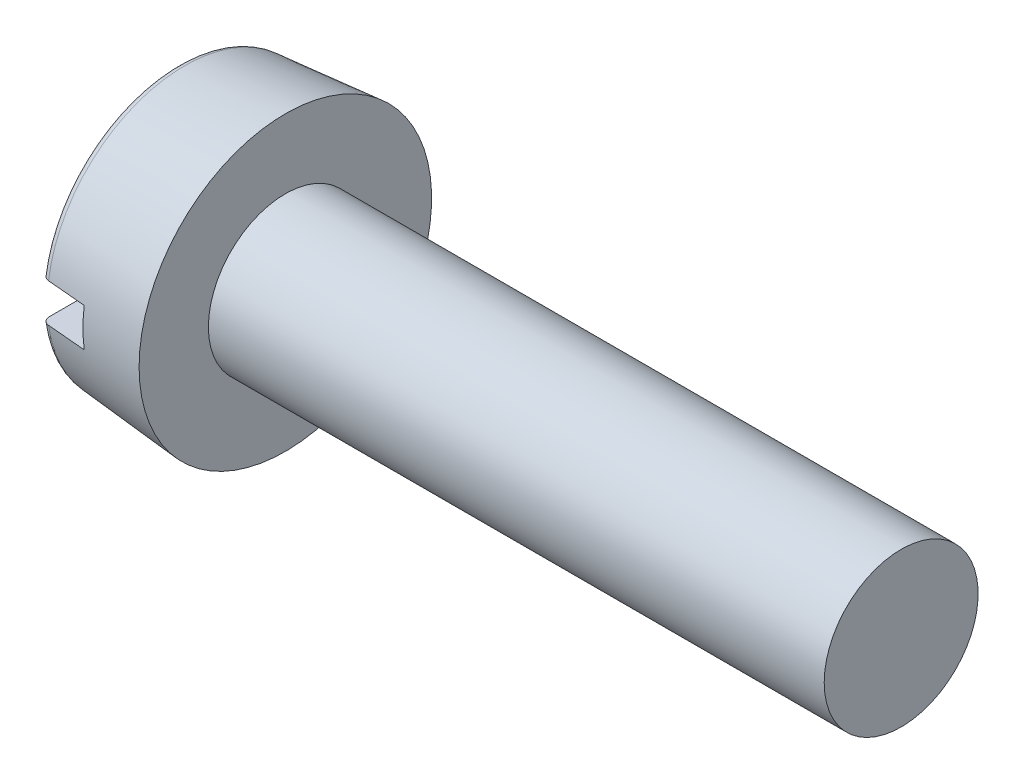
SolidWorks part; units mm, degrees
ref_plane "Plane1" through (0, 0, 0) normal (0, 0, 1) x (1, 0, 0)
ref_plane "Plane2" through (0, 0, 0) normal (0, 1, 0) x (1, 0, 0)
ref_plane "Plane3" through (0, 0, 0) normal (1, 0, 0) x (0, 0, -1)
sketch "BodySke" plane through (0, 0, 0) normal (0, 0, 1) x (1, 0, 0)
  line L0 (1.4, 1) -> (1.4, 1.9)
  line L1 (0, 0) -> (0, 1.7775)
  line L2 (-25.4, 0) -> (127, 0) construction
  line L3 (9.4, 0) -> (0, 0)
  line L4 (1.4, 1) -> (9.4, 1)
  line L5 (9.4, 1) -> (9.4, 0)
  line L6 (0, 1.7775) -> (1.4, 1.9)
  line L9 (1.8, 2.5875) -> (1.8, -6.9375) construction
  line L10 (1.4, 6.35) -> (1.4, -3.175) construction
  dimension "Head_ht" = 1.4
  dimension "Diameter" = 2
  dimension "Length" = 8
  dimension "Head_dia" = 3.8
  dimension "Advance" = 0.4
  dimension "Thread_nom" = 8
  dimension "Head_side_angle" = 5
revolve "Base-Revolve" add sketch "BodySke"
cosmetic thread "ThreadCosmetic" [suppressed]
fillet "Fillet1" [suppressed] radius 0.1
fillet "Fillet2" radius 0.1 1 edges at (0, 0, 1.7775)
sketch "Sketch2" plane through (0, 0, 0) normal (1, 0, 0) x (0, 0, -1)
  line L0 (1.9, -0.25) -> (-1.9, -0.25)
  line L1 (1.9, -0.25) -> (1.9, 0.25)
  line L2 (-1.9, 0.25) -> (1.9, 0.25)
  line L3 (-1.9, 0.25) -> (-1.9, -0.25)
  dimension "D1" = 3.8
  dimension "D2" = 1.9
  dimension "Slot_width" = 0.5
  dimension "D3" = 0.25
extrude "Slot" cut sketch "Sketch2" along normal blind 0.6
sketch "ThdSchSke" plane through (0, 0, 0) normal (0, 0, 1) x (1, 0, 0)
  line L0 (2.2, -0.774) -> (2.0418, -1)
  line L1 (2.2, -0.774) -> (2.3582, -1)
  line L2 (2.3582, -1) -> (2.3582, -1.25)
  line L3 (-3.175, 0) -> (5.1513, 0) construction
  line L5 (2.3582, -1.25) -> (2.0418, -1.25)
  line L6 (2.0418, -1.25) -> (2.0418, -1)
  dimension "Thread_minor" = 1.548
  dimension "Diameter" = 2
  dimension "Start" = 2.2
  dimension "SideAngle" = 55
  dimension "VeeAngle" = 70
  dimension "Overcut" = 2.5
revolve "ThreadSchematic" [suppressed] cut sketch "ThdSchSke" angle 360 about L3
pattern_linear "ThdSchPat" [suppressed]
equation "\"D1@Sketch2\" = \"Head_dia@BodySke\""
equation "\"D2@Sketch2\" = \"D1@Sketch2\" / 2"
equation "\"D3@Sketch2\" = \"Slot_width@Sketch2\" / 2"
equation "\"Thread_length@ThreadCosmetic\" = ((sgn( (\"Length@BodySke\" - \"Advance@BodySke\" * 2.0 ) - \"Thread_nom@BodySke\" )-1)*( (\"Length@BodySke\" - \"Advance@BodySke\"  * 2.0) - \"Thread_nom@BodySke\" ))/-2+ \"Thread_nom@BodySke\""
equation "\"Thread_minor@ThdSchSke\" = \"Thread_minor@ThreadCosmetic\""
equation "\"Diameter@ThdSchSke\" = \"Diameter@BodySke\""
equation "\"Overcut@ThdSchSke\" = \"Diameter@BodySke\" * 1.25"
equation "\"Start@ThdSchSke\" = \"Head_ht@BodySke\" + \"Length@BodySke\" - \"Thread_length@ThreadCosmetic\"  '---Non-countersunk---"
equation "\"Num_threads@ThdSchPat\" = int( \"Thread_length@ThreadCosmetic\" / \"Advance@BodySke\" + 0.999 )  + 1"
equation "\"Advance@ThdSchPat\" = \"Thread_length@ThreadCosmetic\" /  (\"Num_threads@ThdSchPat\" - 1) 'relax it"
